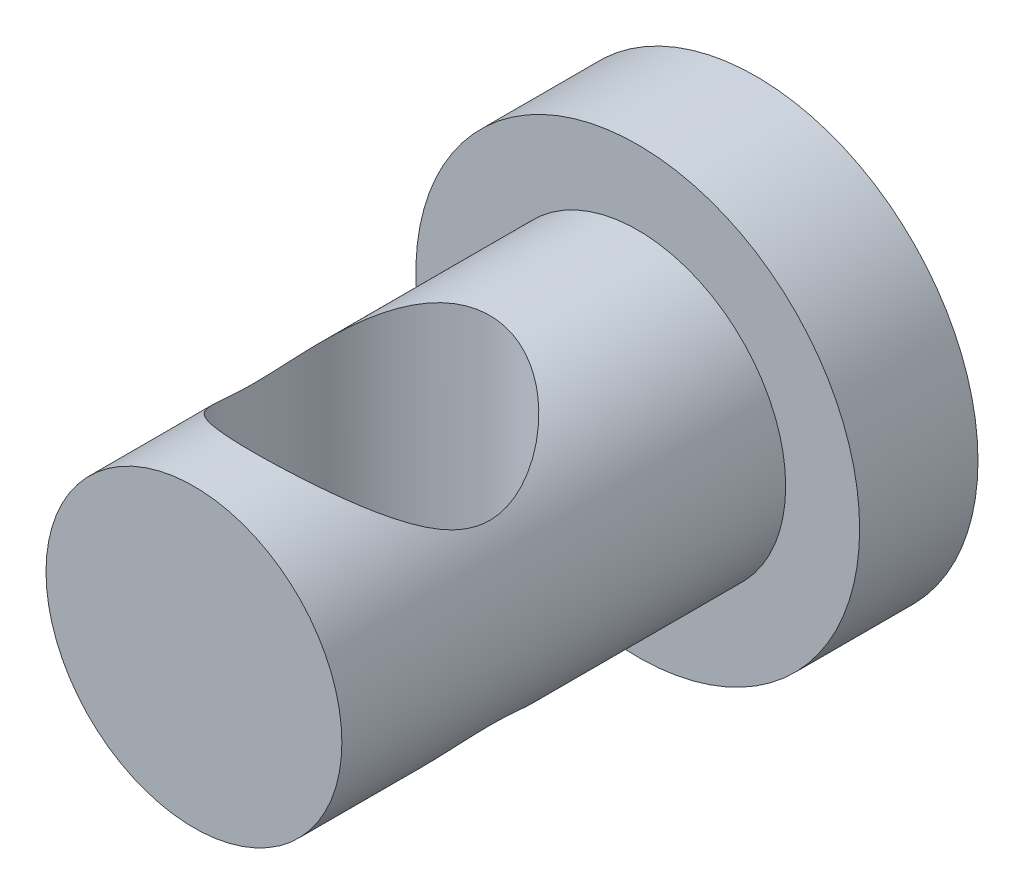
SolidWorks part; units mm, degrees
ref_plane "Front Plane" through (0, 0, 0) normal (0, 0, 1) x (1, 0, 0)
ref_plane "Top Plane" through (0, 0, 0) normal (0, 1, 0) x (1, 0, 0)
ref_plane "Right Plane" through (0, 0, 0) normal (1, 0, 0) x (0, 0, -1)
sketch "Sketch1" plane through (0, 0, 0) normal (0, 0, 1) x (1, 0, 0)
  circle A0 centre (0, 0) radius 7.5
  dimension "D1" = 15
extrude "Boss-Extrude1" add sketch "Sketch1" along normal blind 4
sketch "Sketch2" plane through (0, 0, 4) normal (0, 0, 1) x (1, 0, 0)
  circle A0 centre (0, 0) radius 5
  dimension "D1" = 10
extrude "Boss-Extrude2" add sketch "Sketch2" along normal blind 15
sketch "Sketch3" plane through (0, 0, 0) normal (0, 1, 0) x (1, 0, 0)
  line L0 (-5, -19) -> (5, -19) construction
  line L3 (-5, -4) -> (-5, -19) construction
  circle A0 centre (0, -13) radius 4
  dimension "D1" = 8
  dimension "D3" = 5
  dimension "D2" = 6
extrude "Cut-Extrude1" cut sketch "Sketch3" against normal mid plane 14
